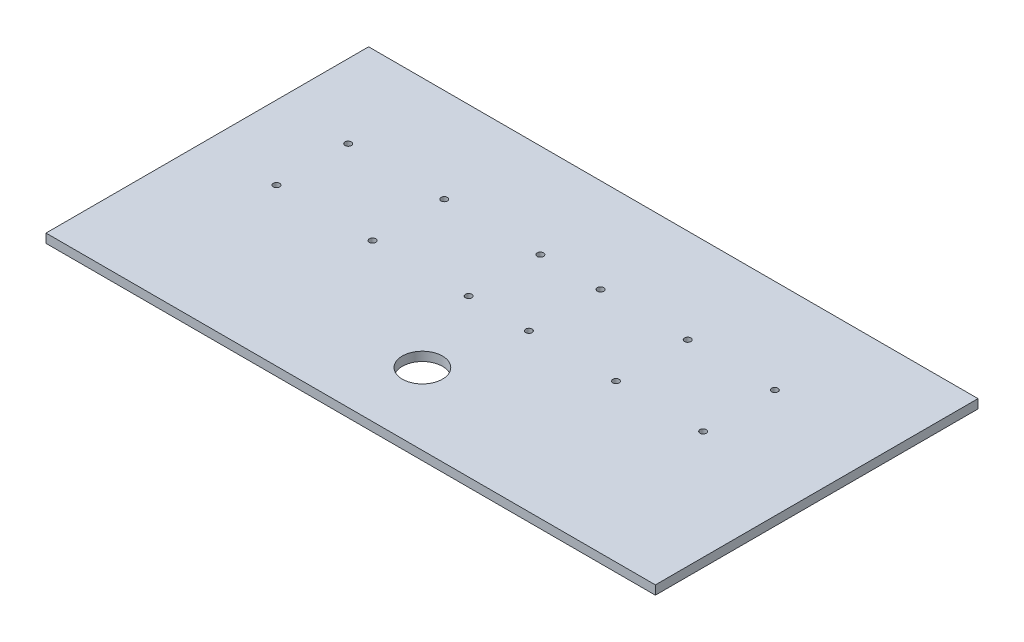
SolidWorks part; units mm, degrees
ref_plane "Front Plane" through (0, 0, 0) normal (0, 0, 1) x (1, 0, 0)
ref_plane "Top Plane" through (0, 0, 0) normal (0, 1, 0) x (1, 0, 0)
ref_plane "Right Plane" through (0, 0, 0) normal (1, 0, 0) x (0, 0, -1)
sketch "Sketch2" plane through (0, 0, 0) normal (0, 1, 0) x (1, 0, 0)
  line L1 (0, 0) -> (431.8, 0)
  line L2 (0, 0) -> (0, 228.6)
  line L3 (0, 228.6) -> (431.8, 228.6)
  line L4 (431.8, 0) -> (431.8, 228.6)
  dimension "D1" = 431.8
  dimension "D2" = 228.6
extrude "Boss-Extrude1" add sketch "Sketch2" along normal blind 6.35
sketch "Sketch4" plane through (0, 6.35, 0) normal (0, 1, 0) x (1, 0, 0)
  line L0 (0, 0) -> (431.8, 0) construction
  line L1 (431.8, 0) -> (431.8, 228.6) construction
  circle A0 centre (215.9, 50.8) radius 14.224
  dimension "D1" = 28.448
  dimension "D2" = 50.8
  dimension "D3" = 215.9
extrude "Cut-Extrude1" cut sketch "Sketch4" against normal blind 6.35
sketch "Sketch5" plane through (0, 0, 0) normal (0, -1, 0) x (-1, 0, 0)
  circle A0 centre (-52.2328, 111.0813) radius 2.2497
  circle A1 centre (-52.2328, 161.8813) radius 2.2497
  dimension "D1" = 4.4994
  dimension "D2" = 4.4994
extrude "Cut-Extrude2" cut sketch "Sketch5" against normal blind 25.4
sketch "Sketch6" plane through (0, 0, 0) normal (0, -1, 0) x (-1, 0, 0)
  circle A0 centre (-120.3149, 111.0813) radius 2.2497
  circle A1 centre (-120.3149, 161.8813) radius 2.2497
  circle A2 centre (-188.397, 111.0813) radius 2.2497
  circle A3 centre (-188.397, 161.8813) radius 2.2497
  dimension "D1" = 4.4994
  dimension "D2" = 4.4994
  dimension "D3" = 4.4993
  dimension "D4" = 4.4993
extrude "Cut-Extrude3" cut sketch "Sketch6" against normal blind 25.4
sketch "Sketch7" plane through (0, 0, 0) normal (0, -1, 0) x (-1, 0, 0)
  circle A0 centre (-231.079, 111.0813) radius 2.2497
  circle A1 centre (-231.079, 161.8813) radius 2.2497
  circle A2 centre (-292.8111, 111.0813) radius 2.2497
  circle A3 centre (-292.8111, 161.8813) radius 2.2497
  circle A4 centre (-354.5432, 111.0813) radius 2.2497
  circle A5 centre (-354.5432, 161.8813) radius 2.2497
  dimension "D1" = 4.4994
  dimension "D2" = 4.4993
  dimension "D3" = 4.4993
  dimension "D4" = 4.4993
  dimension "D5" = 4.4993
  dimension "D6" = 4.4993
extrude "Cut-Extrude4" cut sketch "Sketch7" against normal blind 25.4
